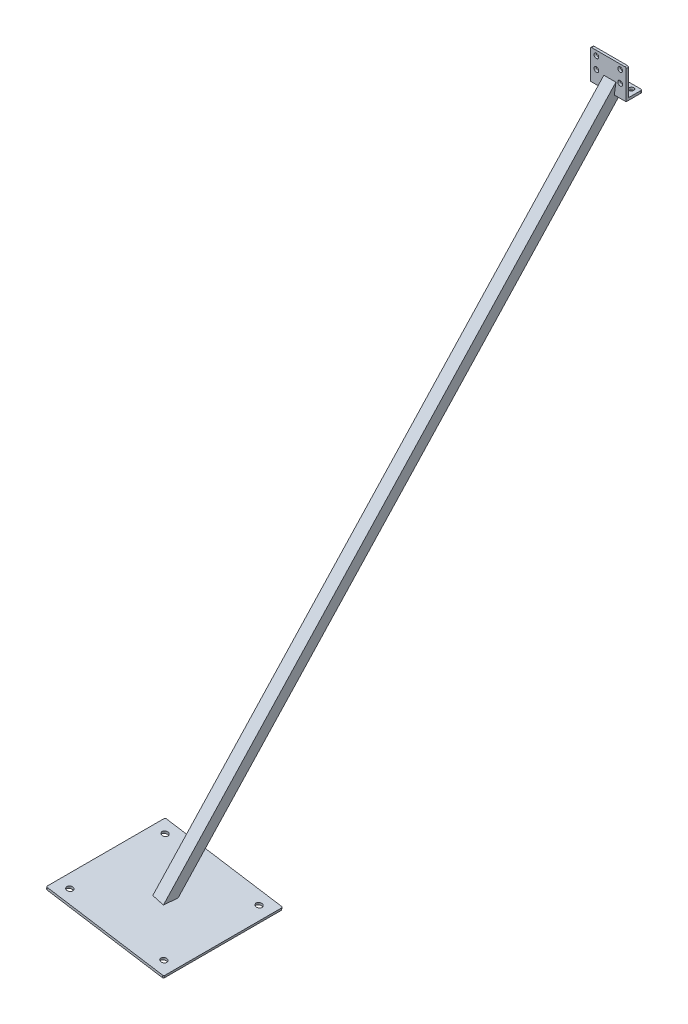
SolidWorks part; units mm, degrees
ref_plane "Front Plane" through (0, 0, 0) normal (0, 0, 1) x (1, 0, 0)
ref_plane "Top Plane" through (0, 0, 0) normal (0, 1, 0) x (1, 0, 0)
ref_plane "Right Plane" through (0, 0, 0) normal (1, 0, 0) x (0, 0, -1)
sketch "Sketch1" plane through (0, 0, 0) normal (1, 0, 0) x (0, 0, -1)
  line L0 (0, 0) -> (0, 50)
  line L1 (0, 50) -> (4, 50)
  line L2 (4, 50) -> (4, 4)
  line L3 (4, 4) -> (27, 4)
  line L4 (27, 4) -> (27, 0)
  line L5 (27, 0) -> (0, 0)
  dimension "D1" = 4
  dimension "D2" = 4
  dimension "D3" = 50
  dimension "D4" = 27
extrude "Boss-Extrude1" add sketch "Sketch1" along normal blind 60
ref_plane "Plane1" through (0, 0, 0) normal (0, -0.866, 0.5) x (-1, 0, 0)
sketch "Sketch2" plane through (0, 0, 0) normal (0, -0.866, 0.5) x (-1, 0, 0)
  line L0 (-30, 0) -> (-30, 23.3827)
  line L1 (-60, 0) -> (0, 0) construction
  line L2 (-60, 23.3827) -> (0, 23.3827) construction
ref_plane "Plane2" through (0.7342, 4.0142, -2.3176) normal (-0.1564, -0.8554, 0.4938) x (0, -0.5, -0.866)
sketch "Sketch3" plane through (0.7342, 4.0142, -2.3176) normal (-0.1564, -0.8554, 0.4938) x (0, -0.5, -0.866)
  line L0 (-9, 38.6307) -> (9, 38.6307)
  line L1 (-10, 39.6307) -> (10, 39.6307)
  line L2 (-10, 39.6307) -> (-10, 19.6307)
  line L3 (-10, 19.6307) -> (10, 19.6307)
  line L4 (10, 39.6307) -> (10, 19.6307)
  line L5 (-10, 39.6307) -> (10, 19.6307) construction
  line L6 (-10, 19.6307) -> (10, 39.6307) construction
  line L7 (9, 38.6307) -> (9, 20.6307)
  line L8 (-9, 20.6307) -> (9, 20.6307)
  line L9 (-9, 38.6307) -> (-9, 20.6307)
  point P0 (0, 29.6307)
  dimension "D1" = 20
  dimension "D2" = 20
  dimension "D3" = 1
extrude "Boss-Extrude2" add sketch "Sketch3" along normal blind 2000 and the other way blind 20
sketch "Sketch4" plane through (0, 0, 0) normal (-1, 0, 0) x (0, 0, 1)
  line L0 (-4, 4) -> (-4, 34.4259)
  line L1 (-4, 4) -> (-4, 50) construction
  line L2 (-4, 34.4259) -> (-31.384, 4)
  line L3 (-27, 4) -> (-4, 4) construction
  line L4 (-31.384, 4) -> (-4, 4)
extrude "Cut-Extrude1" cut sketch "Sketch4" against normal blind 60
ref_plane "Plane3" through (-155.5473, -982.0868, 0) normal (0.1564, 0.9877, 0) x (0.9877, -0.1564, 0)
sketch "Sketch6" plane through (-155.5473, -982.0868, 0) normal (0.1564, 0.9877, 0) x (0.9877, -0.1564, 0)
  line L0 (-2.5847, -997.1308) -> (-22.5192, -995.5664) construction
  line L2 (19.2115, 0) -> (-22.5192, -995.5664) construction
  line L4 (105.477, -466.4414) -> (-94.523, -466.4414)
  line L5 (105.477, -466.4414) -> (105.477, -666.4414)
  line L6 (105.477, -666.4414) -> (-94.523, -666.4414)
  line L7 (-94.523, -466.4414) -> (-94.523, -666.4414)
  line L8 (105.477, -466.4414) -> (-94.523, -666.4414) construction
  line L9 (105.477, -666.4414) -> (-94.523, -466.4414) construction
  point P0 (5.477, -566.4414)
  point P6 (5.477, -566.4414)
  dimension "D1" = 430
  dimension "D2" = 10
  dimension "D3" = 200
  dimension "D4" = 200
extrude "Boss-Extrude3" add sketch "Sketch6" along normal blind 4
sketch "Sketch7" plane through (-155.5473, -982.0868, 0) normal (-0.1564, -0.9877, 0) x (0.9877, -0.1564, 0)
  line L1 (-84.9465, 1031.7358) -> (70.9442, 1031.7358)
  line L2 (-84.9465, 1031.7358) -> (-84.9465, 540.4439)
  line L3 (-84.9465, 540.4439) -> (70.9442, 540.4439)
  line L4 (70.9442, 1031.7358) -> (70.9442, 540.4439)
extrude "Cut-Extrude2" cut sketch "Sketch7" along normal blind 1000
sketch "Sketch8" plane through (0, 0, 0) normal (0, 0, 1) x (1, 0, 0)
  circle A0 centre (10, 22) radius 4 construction
  circle A1 centre (50, 22) radius 4 construction
  circle A2 centre (50, 42) radius 4 construction
  circle A3 centre (10, 42) radius 4 construction
  circle A4 centre (10, 22) radius 4
  circle A5 centre (50, 22) radius 4
  circle A6 centre (50, 42) radius 4
  circle A7 centre (10, 42) radius 4
extrude "Cut-Extrude3" cut sketch "Sketch8" against normal up to next
sketch "Sketch9" plane through (0, 0, 0) normal (0, -1, 0) x (1, 0, 0)
  circle A0 centre (50, -19) radius 4 construction
  circle A1 centre (10, -19) radius 4 construction
  circle A2 centre (50, -19) radius 4
  circle A3 centre (10, -19) radius 4
extrude "Cut-Extrude4" cut sketch "Sketch9" against normal up to next
sketch "Sketch10" plane through (-155.5473, -982.0868, 0) normal (-0.1564, -0.9877, 0) x (0.9877, -0.1564, 0)
  line L0 (-94.523, 666.4414) -> (105.477, 666.4414) construction
  line L1 (-94.523, 466.4414) -> (-94.523, 666.4414) construction
  circle A0 centre (-74.523, 646.4414) radius 5
  circle A1 centre (85.477, 646.4414) radius 5
  circle A2 centre (85.477, 486.4414) radius 5
  circle A3 centre (-74.523, 486.4414) radius 5
  dimension "D1" = 10
  dimension "D2" = 20
  dimension "D3" = 20
  dimension "D6" = 160
  dimension "D7" = 160
  dimension "D4" = 2
  dimension "D5" = 2
extrude "Cut-Extrude5" cut sketch "Sketch10" against normal up to next
fillet "Fillet1" radius 2 4 edges at (-248.5936, -965.3247, 666.4414) (-248.5936, -965.3247, 466.4414) (-51.056, -996.6116, 466.4414) (-51.056, -996.6116, 666.4414)
fillet "Fillet2" radius 2 4 edges at (60, 2, -27) (0, 2, -27) (60, 50, -2) (0, 50, -2)
